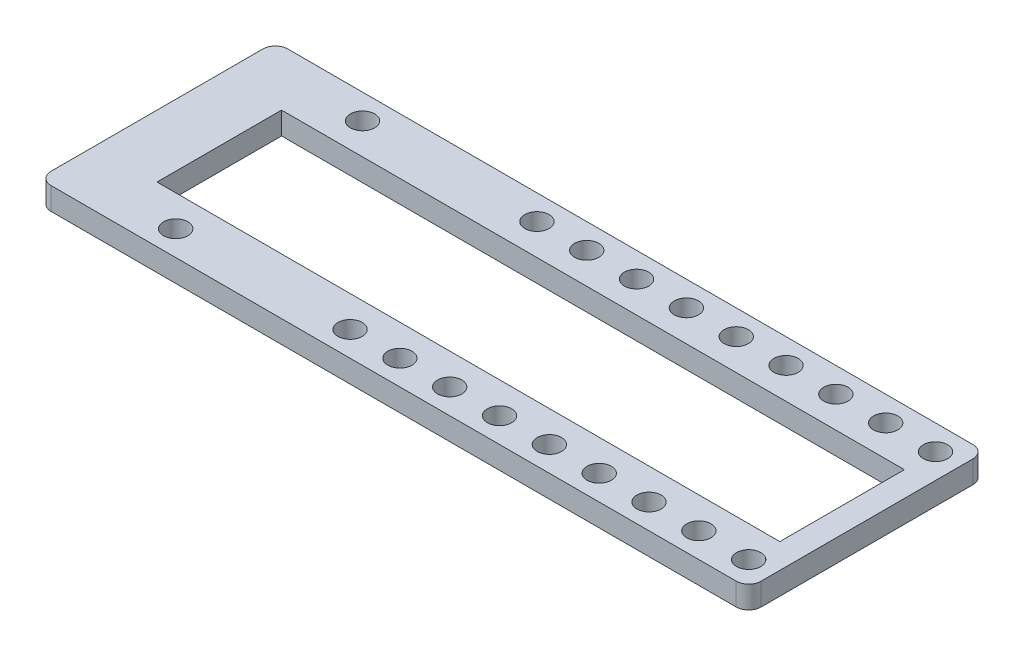
SolidWorks part; units mm, degrees
ref_plane "Front Plane" through (0, 0, 0) normal (0, 0, 1) x (1, 0, 0)
ref_plane "Top Plane" through (0, 0, 0) normal (0, 1, 0) x (1, 0, 0)
ref_plane "Right Plane" through (0, 0, 0) normal (1, 0, 0) x (0, 0, -1)
sketch "Sketch1" plane through (0, 0, 0) normal (0, 1, 0) x (1, 0, 0)
  line L1 (2, 0) -> (112, 0)
  line L2 (0, -2) -> (0, -36)
  line L3 (2, -38) -> (112, -38)
  line L4 (114, -2) -> (114, -36)
  arc A0 (112, -38) -> (114, -36) centre (112, -36) ccw
  arc A1 (0, -36) -> (2, -38) centre (2, -36) ccw
  arc A2 (2, 0) -> (0, -2) centre (2, -2) ccw
  arc A3 (112, 0) -> (114, -2) centre (112, -2) cw
  point P7 (114, -38)
  point P12 (0, 0)
  point P15 (114, 0)
  dimension "D3" = 2
  dimension "D1" = 114
  dimension "D2" = 38
extrude "Boss-Extrude1" add sketch "Sketch1" along normal blind 3.6
sketch "Sketch2" plane through (0, 3.6, 0) normal (0, 1, 0) x (1, 0, 0)
  line L0 (112, 0) -> (2, 0) construction
  line L1 (114, -36) -> (114, -2) construction
  line L2 (110, -4) -> (0, -4) construction
  line L3 (0, -2) -> (0, -36) construction
  line L4 (110, -34) -> (0, -34) construction
  line L5 (2, -38) -> (112, -38) construction
  line L7 (10, -9) -> (110, -9)
  line L8 (10, -9) -> (10, -29)
  line L9 (10, -29) -> (110, -29)
  line L10 (110, -9) -> (110, -29)
  circle A0 centre (110, -4) radius 1.95
  circle A1 centre (102, -4) radius 1.95
  circle A2 centre (18, -4) radius 1.95
  circle A3 centre (46, -4) radius 1.95
  circle A4 centre (54, -4) radius 1.95
  circle A5 centre (62, -4) radius 1.95
  circle A6 centre (70, -4) radius 1.95
  circle A7 centre (78, -4) radius 1.95
  circle A8 centre (86, -4) radius 1.95
  circle A9 centre (94, -4) radius 1.95
  circle A10 centre (110, -34) radius 1.95
  circle A11 centre (102, -34) radius 1.95
  circle A12 centre (18, -34) radius 1.95
  circle A13 centre (46, -34) radius 1.95
  circle A14 centre (54, -34) radius 1.95
  circle A15 centre (62, -34) radius 1.95
  circle A16 centre (70, -34) radius 1.95
  circle A17 centre (78, -34) radius 1.95
  circle A18 centre (86, -34) radius 1.95
  circle A19 centre (94, -34) radius 1.95
  dimension "D1" = 3.9
  dimension "D4" = 3.9
  dimension "D7" = 3.9
  dimension "D8" = 3.9
  dimension "D9" = 3.9
  dimension "D10" = 3.9
  dimension "D11" = 3.9
  dimension "D12" = 3.9
  dimension "D13" = 3.9
  dimension "D14" = 3.9
  dimension "D22" = 3.9
  dimension "D23" = 3.9
  dimension "D25" = 3.9
  dimension "D26" = 3.9
  dimension "D27" = 3.9
  dimension "D28" = 3.9
  dimension "D29" = 3.9
  dimension "D30" = 3.9
  dimension "D31" = 3.9
  dimension "D32" = 3.9
  dimension "D3" = 4
  dimension "D5" = 8
  dimension "D6" = 18
  dimension "D15" = 8
  dimension "D16" = 8
  dimension "D17" = 8
  dimension "D18" = 8
  dimension "D19" = 8
  dimension "D20" = 8
  dimension "D21" = 8
  dimension "D24" = 8
  dimension "D33" = 8
  dimension "D34" = 8
  dimension "D35" = 8
  dimension "D36" = 8
  dimension "D37" = 8
  dimension "D38" = 8
  dimension "D39" = 8
  dimension "D40" = 5
  dimension "D41" = 4
  dimension "D42" = 18
  dimension "D43" = 4
  dimension "D44" = 9
  dimension "D45" = 10
  dimension "D46" = 9
  dimension "D47" = 5
extrude "Cut-Extrude1" cut sketch "Sketch2" against normal blind 3.6
